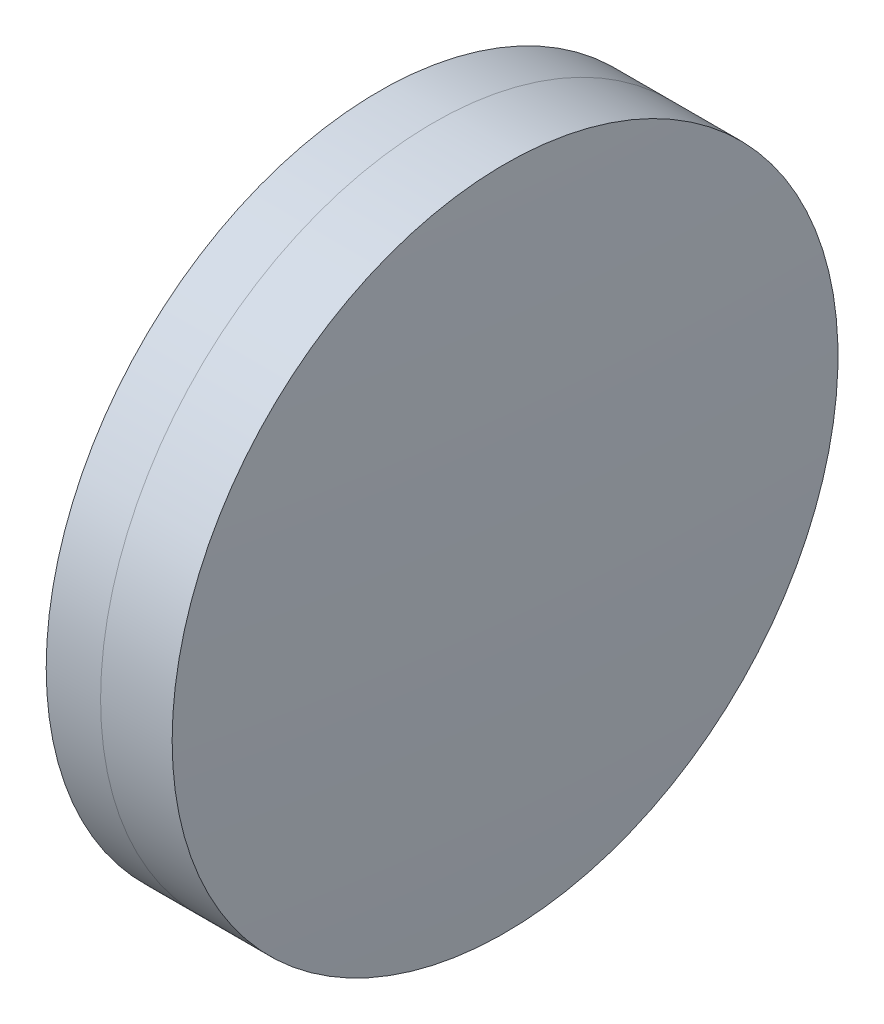
SolidWorks part; units mm, degrees
ref_plane "前视基准面" through (0, 0, 0) normal (0, 0, 1) x (1, 0, 0)
ref_plane "上视基准面" through (0, 0, 0) normal (0, 1, 0) x (1, 0, 0)
ref_plane "右视基准面" through (0, 0, 0) normal (1, 0, 0) x (0, 0, -1)
sketch "草图1" plane through (0, 0, 0) normal (0, 1, 0) x (1, 0, 0)
  line L0 (-9.7026, 0) -> (115.8928, 0) construction
  line L1 (91.8702, -12.5) -> (93.9123, -12.5)
  line L2 (91.8702, 12.5) -> (93.9123, 12.5)
  arc A0 (93.9123, -12.5) -> (93.9123, 12.5) centre (14.8797, 0) ccw
  arc A1 (91.8702, 12.5) -> (91.8702, -12.5) centre (216.4447, 0) ccw
  point P4 (115.8928, 0)
  point P10 (91.2447, 0)
  point P11 (94.8947, 0)
  dimension "D3" = 125.2
  dimension "D4" = 80.015
  dimension "D1" = 12.5
  dimension "D2" = 12.5
  dimension "D5" = 3.65
revolve "旋转1" add sketch "草图1" angle 360 about L0
sketch "草图2" plane through (0, 0, 0) normal (0, 1, 0) x (1, 0, 0)
  line L0 (-0.5519, 0) -> (103.414, 0) construction
  line L2 (93.9123, 12.5) -> (96.5993, 12.5)
  line L3 (93.9123, -12.5) -> (96.5993, -12.5)
  arc A0 (96.5993, -12.5) -> (96.5993, 12.5) centre (-159.1073, 0) ccw
  arc A1 (93.9123, -12.5) -> (93.9123, 12.5) centre (14.8797, 0) ccw construction
  arc A2 (93.9123, -12.5) -> (93.9123, 12.5) centre (14.8797, 0) ccw
  point P4 (94.8947, 0)
  point P8 (96.9047, 0)
  point P9 (103.414, 0)
  dimension "D1" = 256.012
  dimension "D2" = 2.01
revolve "旋转3" add sketch "草图2" angle 360 about L0
